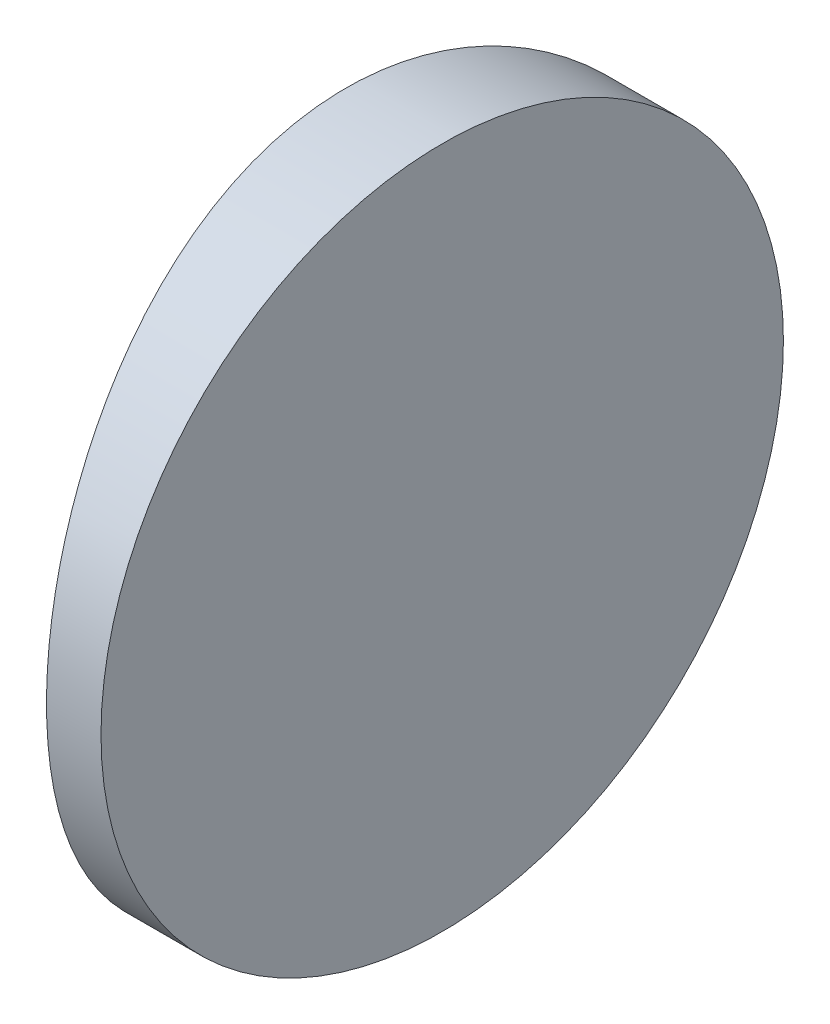
SolidWorks part; units mm, degrees
ref_plane "前视基准面" through (0, 0, 0) normal (0, 0, 1) x (1, 0, 0)
ref_plane "上视基准面" through (0, 0, 0) normal (0, 1, 0) x (1, 0, 0)
ref_plane "右视基准面" through (0, 0, 0) normal (1, 0, 0) x (0, 0, -1)
sketch "草图1" plane through (0, 0, 0) normal (0, 1, 0) x (1, 0, 0)
  line L0 (10.7432, 0) -> (-55.502, 0) construction
  line L1 (-45.7903, 12.5) -> (-43.7948, 12.5)
  line L2 (-45.7903, -12.5) -> (-43.7948, -12.5)
  line L3 (-43.7948, 12.5) -> (-43.7948, -12.5)
  arc A0 (-45.7903, 12.5) -> (-45.7903, -12.5) centre (4.3552, 0) ccw
  point P19 (-47.3248, 0)
  point P20 (-43.7948, 0)
  dimension "D2" = 12.5
  dimension "D3" = 51.68
  dimension "D4" = 3.53
  dimension "D1" = 12.5
extrude "凸台-拉伸1" add sketch "草图1" along normal blind 25 contours A0 L2 L3 L1
sketch "草图2" plane through (-43.7948, 0, 0) normal (1, 0, 0) x (0, 0, -1)
  line L0 (12.5, 0) -> (-12.5, 0) construction
  line L7 (-12.5, 0) -> (12.5, 0)
  line L8 (12.5, 0) -> (12.5, 25)
  line L9 (12.5, 25) -> (-12.5, 25)
  line L10 (-12.5, 25) -> (-12.5, 0)
  line L11 (-12.5, 0) -> (12.5, 0)
  line L12 (12.5, 0) -> (12.5, 25)
  line L13 (12.5, 25) -> (-12.5, 25)
  line L14 (-12.5, 25) -> (-12.5, 0)
  circle A0 centre (0, 12.5) radius 12.5
  line M1 (-12.5, 0) -> (12.5, 0)
  line M2 (12.5, 0) -> (12.5, 25)
  line M3 (12.5, 25) -> (-12.5, 25)
  line M4 (-12.5, 25) -> (-12.5, 0)
  dimension "D1" = 25
  dimension "D4" = 12.5
  dimension "D2" = 12.5
  dimension "D3" = 0
extrude "切除-拉伸8" cut sketch "草图2" against normal blind 12.7 contours A0 L13 M4 | A0 L12 M3 | A0 L11 M2 | A0 L14 M1
